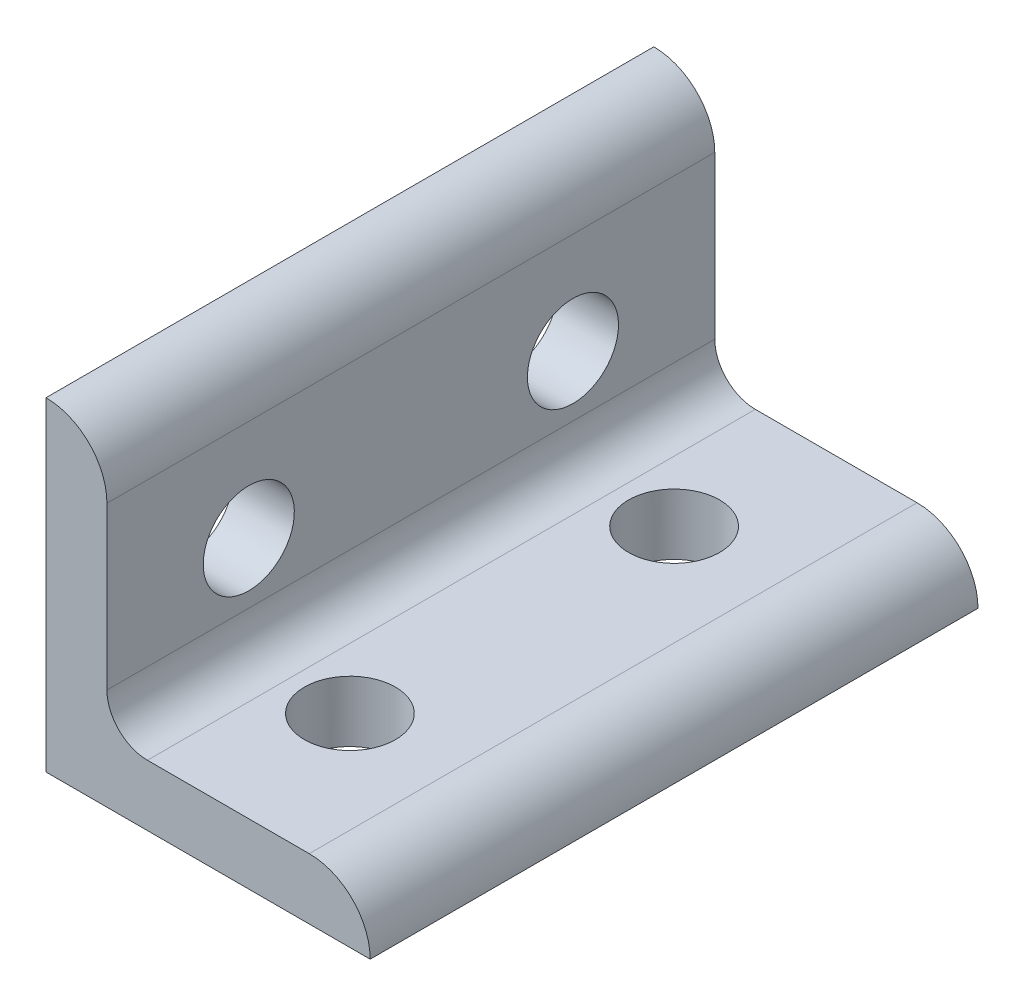
SolidWorks part; units mm, degrees
ref_plane "Front Plane" through (0, 0, 0) normal (0, 0, 1) x (1, 0, 0)
ref_plane "Top Plane" through (0, 0, 0) normal (0, 1, 0) x (1, 0, 0)
ref_plane "Right Plane" through (0, 0, 0) normal (1, 0, 0) x (0, 0, -1)
sketch "Sketch1" plane through (0, 0, 0) normal (0, 0, 1) x (1, 0, 0)
  line L0 (0, 0) -> (0, 25.4)
  line L1 (4.7752, 20.6248) -> (4.7752, 25.4) construction
  line L2 (4.7752, 20.6248) -> (4.7752, 7.9502)
  line L3 (7.9502, 4.7752) -> (20.6248, 4.7752)
  line L4 (4.7752, 25.4) -> (0, 25.4) construction
  line L5 (25.4, 0) -> (0, 0)
  line L6 (20.6248, 4.7752) -> (25.4, 4.7752) construction
  line L7 (25.4, 4.7752) -> (25.4, 0) construction
  arc A0 (4.7752, 20.6248) -> (0, 25.4) centre (0, 20.6248) ccw
  arc A1 (25.4, 0) -> (20.6248, 4.7752) centre (20.6248, 0) ccw
  arc A2 (4.7752, 7.9502) -> (7.9502, 4.7752) centre (7.9502, 7.9502) ccw
  point P10 (4.7752, 23.0124)
  dimension "E" = 3.175
  dimension "D" = 4.7752
  dimension "C" = 25.4
  dimension "B" = 25.4
extrude "Boss-Extrude1" add sketch "Sketch1" along normal mid plane 47.625
sketch "Sketch2" plane through (0, 0, 0) normal (0, 1, 0) x (1, 0, 0)
  line L0 (0, -12.7) -> (12.7, -12.7) construction
  line L1 (12.7, -12.7) -> (12.7, 12.7) construction
  line L2 (0, -12.7) -> (0, -23.8125) construction
  line L3 (12.7, 12.7) -> (0, 12.7) construction
  line L4 (0, 12.7) -> (0, -12.7) construction
  circle A0 centre (12.7, -12.7) radius 3.5687
  circle A1 centre (12.7, 12.7) radius 3.5687
extrude "Cut-Extrude1" cut sketch "Sketch2" along normal through all
sketch "Sketch3" plane through (0, 0, 0) normal (1, 0, 0) x (0, 0, -1)
  line L0 (-12.7, 0) -> (-12.7, 12.7) construction
  line L2 (12.7, 0) -> (12.7, 12.7) construction
  line L3 (12.7, 12.7) -> (-12.7, 12.7) construction
  circle A0 centre (-12.7, 12.7) radius 3.5687
  circle A1 centre (12.7, 12.7) radius 3.5687
  dimension "D1" = 12.7
extrude "Cut-Extrude2" cut sketch "Sketch3" along normal through all
equation "\"E@Sketch3\" = \"E@Sketch2\""
equation "\"D1@Sketch3\" = \"D1@Sketch2\""
